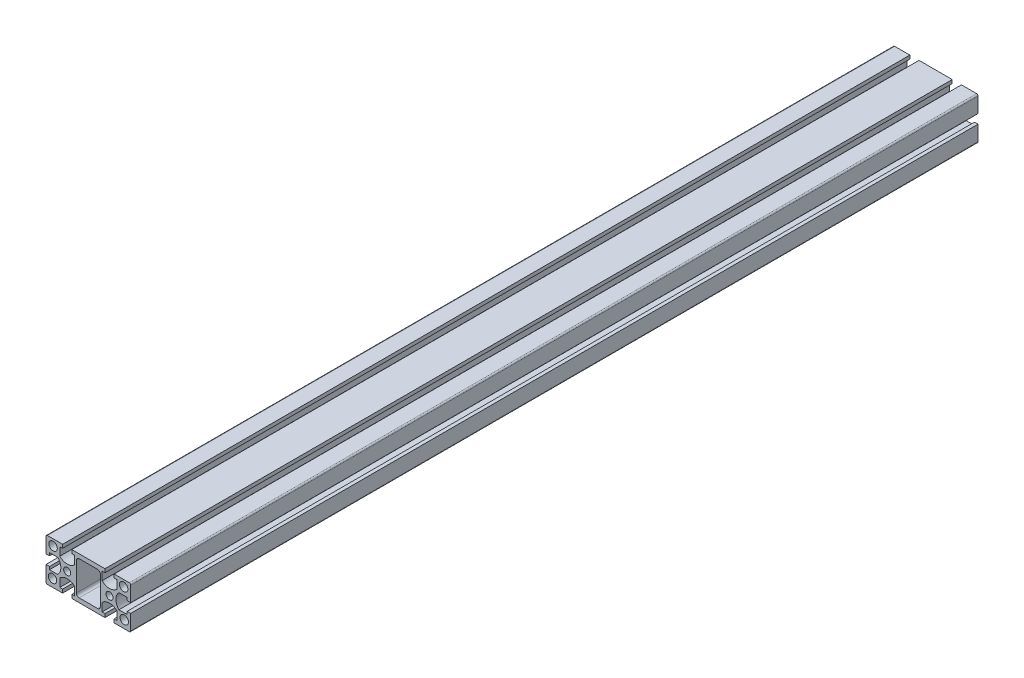
SolidWorks part; units mm, degrees
ref_plane "Front Plane" through (0, 0, 0) normal (0, 0, 1) x (1, 0, 0)
ref_plane "Top Plane" through (0, 0, 0) normal (0, 1, 0) x (1, 0, 0)
ref_plane "Right Plane" through (0, 0, 0) normal (1, 0, 0) x (0, 0, -1)
sketch "Model" plane through (0, 0, 0) normal (0, 0, 1) x (1, 0, 0)
  line L0 (6.5, 12) -> (-6.5, 12)
  line L1 (8.5, 10) -> (8.5, -10)
  line L2 (6.5, -12) -> (-6.5, -12)
  line L3 (-8.5, 10) -> (-8.5, -10)
  line L4 (-27.5, 3.25) -> (-30, 3.25)
  line L5 (-30, -3.25) -> (-27.5, -3.25)
  line L6 (-21.6439, 5.25) -> (-27.5, 5.25)
  line L7 (-27.5, 5.25) -> (-27.5, 3.25)
  line L8 (-21.6439, -5.25) -> (-27.5, -5.25)
  line L9 (-27.5, -5.25) -> (-27.5, -3.25)
  line L10 (-18.25, 15) -> (-18.25, 12.5)
  line L11 (-20.25, 12.5) -> (-18.25, 12.5)
  line L12 (-20.25, 6.6439) -> (-20.25, 12.5)
  line L13 (-9.75, 6.6439) -> (-9.75, 12.5)
  line L14 (-9.75, 12.5) -> (-11.75, 12.5)
  line L15 (-11.75, 12.5) -> (-11.75, 15)
  line L16 (-11.75, -15) -> (-11.75, -12.5)
  line L17 (-9.75, -12.5) -> (-11.75, -12.5)
  line L18 (-9.75, -6.6439) -> (-9.75, -12.5)
  line L19 (-20.25, -6.6439) -> (-20.25, -12.5)
  line L20 (-20.25, -12.5) -> (-18.25, -12.5)
  line L21 (-18.25, -12.5) -> (-18.25, -15)
  line L22 (18.25, -12.5) -> (18.25, -15)
  line L23 (20.25, -12.5) -> (18.25, -12.5)
  line L24 (20.25, -6.6439) -> (20.25, -12.5)
  line L25 (9.75, -6.6439) -> (9.75, -12.5)
  line L26 (9.75, -12.5) -> (11.75, -12.5)
  line L27 (11.75, -15) -> (11.75, -12.5)
  line L28 (27.5, 3.25) -> (30, 3.25)
  line L29 (27.5, 5.25) -> (27.5, 3.25)
  line L30 (21.6439, 5.25) -> (27.5, 5.25)
  line L31 (21.6439, -5.25) -> (27.5, -5.25)
  line L32 (27.5, -5.25) -> (27.5, -3.25)
  line L33 (30, -3.25) -> (27.5, -3.25)
  line L34 (11.75, 12.5) -> (11.75, 15)
  line L35 (9.75, 12.5) -> (11.75, 12.5)
  line L36 (9.75, 6.6439) -> (9.75, 12.5)
  line L37 (20.25, 6.6439) -> (20.25, 12.5)
  line L38 (20.25, 12.5) -> (18.25, 12.5)
  line L39 (18.25, 15) -> (18.25, 12.5)
  line L40 (-18.25, 15) -> (-29, 15)
  line L41 (-30, 14) -> (-30, 3.25)
  line L42 (-30, -3.25) -> (-30, -14)
  line L43 (-29, -15) -> (-18.25, -15)
  line L44 (-11.75, -15) -> (11.75, -15)
  line L45 (18.25, -15) -> (29, -15)
  line L46 (30, -14) -> (30, -3.25)
  line L47 (30, 3.25) -> (30, 14)
  line L48 (29, 15) -> (18.25, 15)
  line L49 (11.75, 15) -> (-11.75, 15)
  circle A0 centre (-15, 0) radius 2.5
  circle A1 centre (-25, 10.5314) radius 3
  circle A2 centre (-25.3993, -9.4686) radius 3
  arc A3 (-21.6439, -5.25) -> (-21.6439, 5.25) centre (-27, 0) ccw
  arc A4 (-20.25, 6.6439) -> (-9.75, 6.6439) centre (-15, 12) ccw
  arc A5 (-9.75, -6.6439) -> (-20.25, -6.6439) centre (-15, -12) ccw
  circle A6 centre (25.3993, -9.4686) radius 3
  arc A7 (20.25, -6.6439) -> (9.75, -6.6439) centre (15, -12) ccw
  circle A8 centre (15, 0) radius 2.5
  arc A9 (21.6439, 5.25) -> (21.6439, -5.25) centre (27, 0) ccw
  circle A10 centre (25, 10.5314) radius 3
  arc A11 (9.75, 6.6439) -> (20.25, 6.6439) centre (15, 12) ccw
  arc A12 (30, 14) -> (29, 15) centre (29, 14) ccw
  arc A13 (29, -15) -> (30, -14) centre (29, -14) ccw
  arc A14 (-30, -14) -> (-29, -15) centre (-29, -14) ccw
  arc A15 (-29, 15) -> (-30, 14) centre (-29, 14) ccw
  arc A16 (-8.5, -10) -> (-6.5, -12) centre (-6.5, -10) ccw
  arc A17 (6.5, -12) -> (8.5, -10) centre (6.5, -10) ccw
  arc A18 (8.5, 10) -> (6.5, 12) centre (6.5, 10) ccw
  arc A19 (-6.5, 12) -> (-8.5, 10) centre (-6.5, 10) ccw
  point P90 (0, 0)
  point P91 (0, 0)
extrude "Boss-Extrude1" add sketch "Model" along normal blind 600
